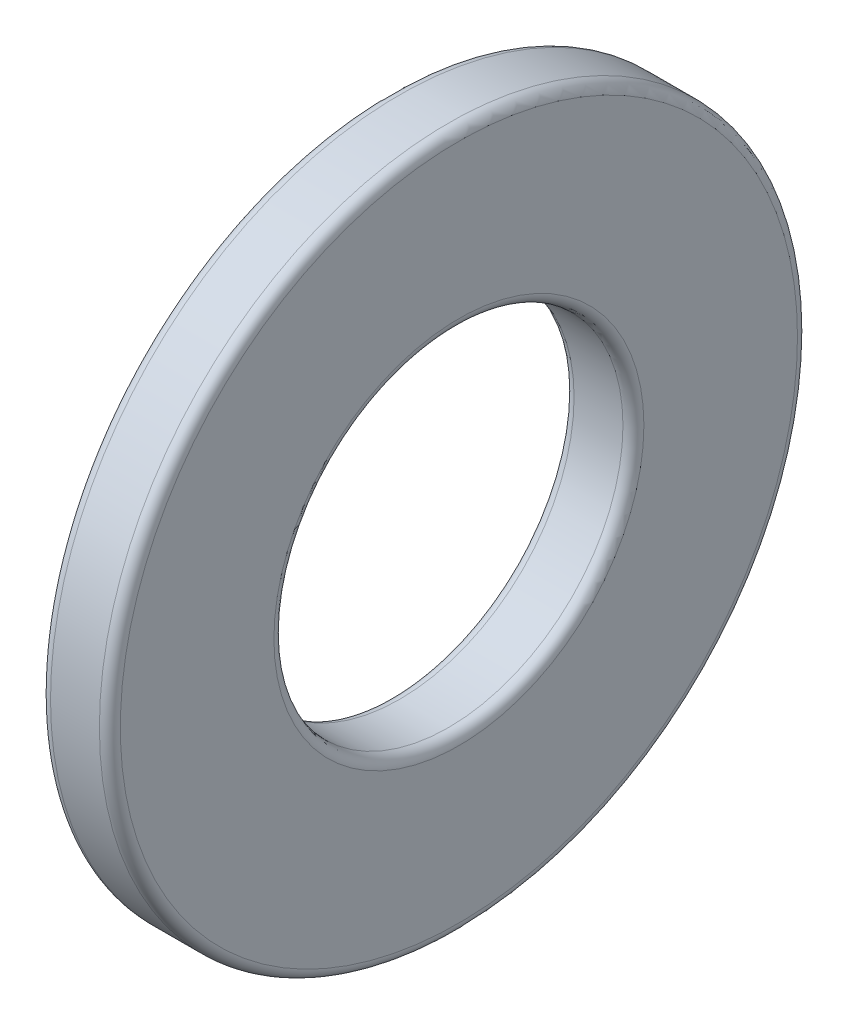
SolidWorks part; units mm, degrees
ref_plane "Front Plane" through (0, 0, 0) normal (0, 0, 1) x (1, 0, 0)
ref_plane "Top Plane" through (0, 0, 0) normal (0, 1, 0) x (1, 0, 0)
ref_plane "Right Plane" through (0, 0, 0) normal (1, 0, 0) x (0, 0, -1)
sketch "Sketch1" plane through (0, 0, 0) normal (1, 0, 0) x (0, 0, -1)
  circle A0 centre (0, 0) radius 2.5
  circle A1 centre (0, 0) radius 5
  dimension "D1" = 10
  dimension "D2" = 5
extrude "Boss-Extrude1" add sketch "Sketch1" along normal blind 1
fillet "Fillet1" radius 0.15 4 edges at (0, 0, -2.5) (0, 0, -5) (1, 0, -2.5) (1, 0, -5)
